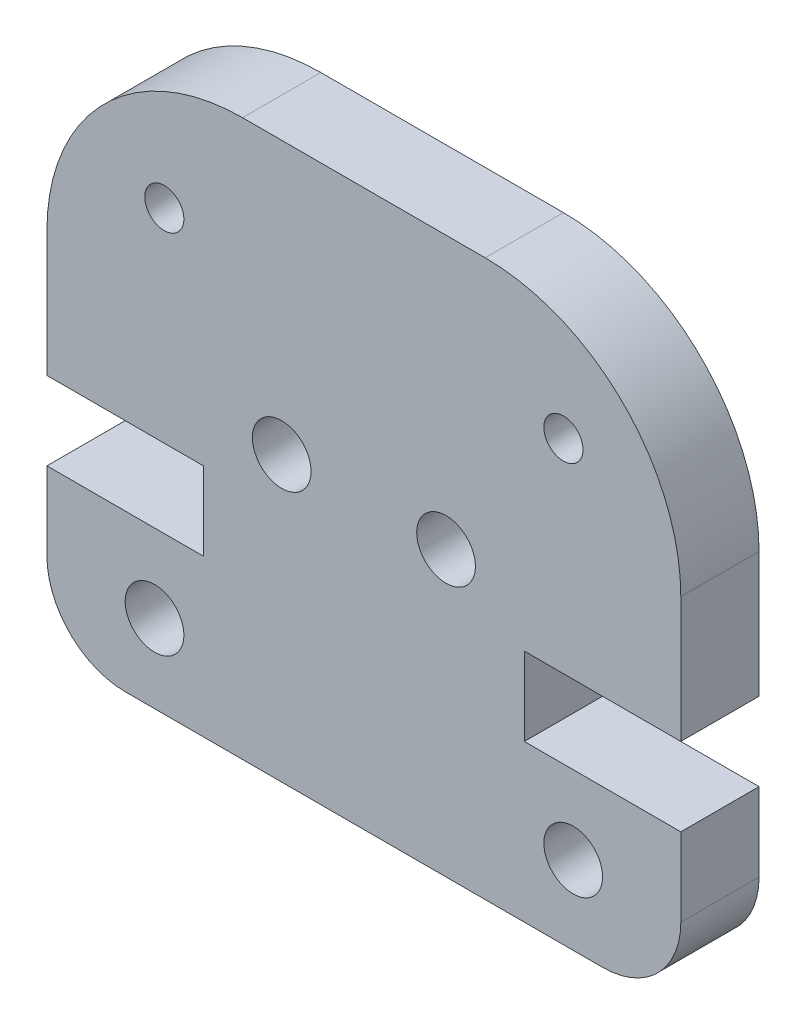
SolidWorks part; units mm, degrees
ref_plane "Front Plane" through (0, 0, 0) normal (0, 0, 1) x (1, 0, 0)
ref_plane "Top Plane" through (0, 0, 0) normal (0, 1, 0) x (1, 0, 0)
ref_plane "Right Plane" through (0, 0, 0) normal (1, 0, 0) x (0, 0, -1)
sketch "Sketch1" plane through (0, 0, 0) normal (0, 0, 1) x (1, 0, 0)
  line L0 (8.1, 14.205) -> (8.1, 0) construction
  line L1 (12.2, 4) -> (16.2, 4)
  line L2 (12.2, 6) -> (12.2, 4)
  line L3 (16.2, 6) -> (12.2, 6)
  line L4 (16.2, 2) -> (16.2, 4)
  line L5 (16.2, 9.205) -> (16.2, 6)
  line L14 (0, 9.205) -> (0, 6)
  line L15 (5, 14.205) -> (11.2, 14.205)
  line L16 (2, 0) -> (14.2, 0)
  line L18 (0, 2) -> (0, 4)
  line L19 (0, 6) -> (4, 6)
  line L21 (4, 6) -> (4, 4)
  line L22 (4, 4) -> (0, 4)
  circle A0 centre (13.45, 2) radius 0.75
  arc A1 (16.2, 2) -> (14.2, 0) centre (14.2, 2) cw
  circle A2 centre (13.2, 11.205) radius 0.5
  arc A3 (11.2, 14.205) -> (16.2, 9.205) centre (11.2, 9.205) cw
  circle A4 centre (10.2, 7.25) radius 0.75
  circle A11 centre (6, 7.25) radius 0.75
  arc A13 (5, 14.205) -> (0, 9.205) centre (5, 9.205) ccw
  circle A15 centre (3, 11.205) radius 0.5
  arc A17 (0, 2) -> (2, 0) centre (2, 2) ccw
  circle A19 centre (2.75, 2) radius 0.75
  dimension "D1" = 1
  dimension "D2" = 1.5
  dimension "D3" = 5
  dimension "D4" = 2
  dimension "D5" = 3
  dimension "D6" = 6
  dimension "D7" = 8.1
  dimension "D8" = 7.25
  dimension "D9" = 3
  dimension "D10" = 14.205
extrude "Boss-Extrude1" add sketch "Sketch1" along normal blind 2
equation "\"D7@Sketch1\"= \"fingerWidth@parametersSketch@prostheticParameters.SLDPRT\" / 2 'DIP width"
equation "\"D10@Sketch1\"= \"HL@parametersSketch@prostheticParameters.SLDPRT\" * 0.093 - 3 'DIP length - Sil. Sht DIP"
